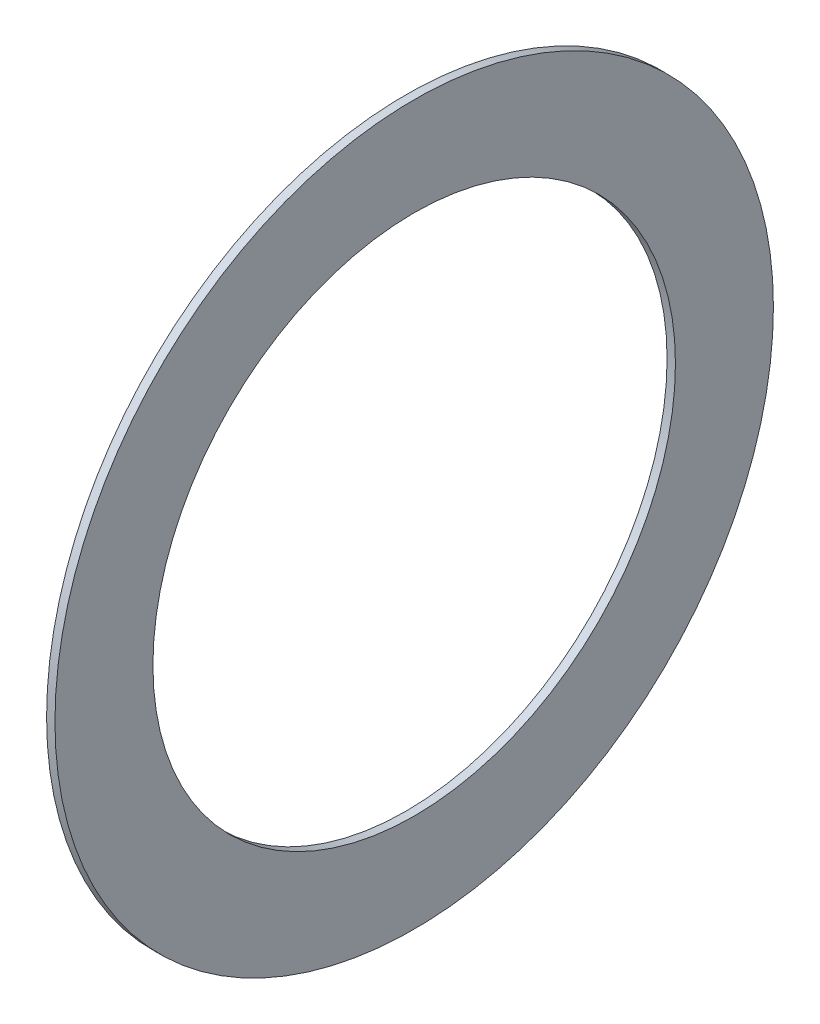
SolidWorks part; units mm, degrees
material "Alloy Steel"
ref_plane "Front Plane" through (0, 0, 0) normal (0, 0, 1) x (1, 0, 0)
ref_plane "Top Plane" through (0, 0, 0) normal (0, 1, 0) x (1, 0, 0)
ref_plane "Right Plane" through (0, 0, 0) normal (1, 0, 0) x (0, 0, -1)
sketch "Sketch1" plane through (0, 0, 0) normal (1, 0, 0) x (0, 0, -1)
  circle A0 centre (0, 0) radius 34.925
  circle A1 centre (0, 0) radius 25.4
  dimension "OD" = 69.85
  dimension "Shaft Dia" = 50.8
extrude "Extrude1" add sketch "Sketch1" along normal blind 0.8128
